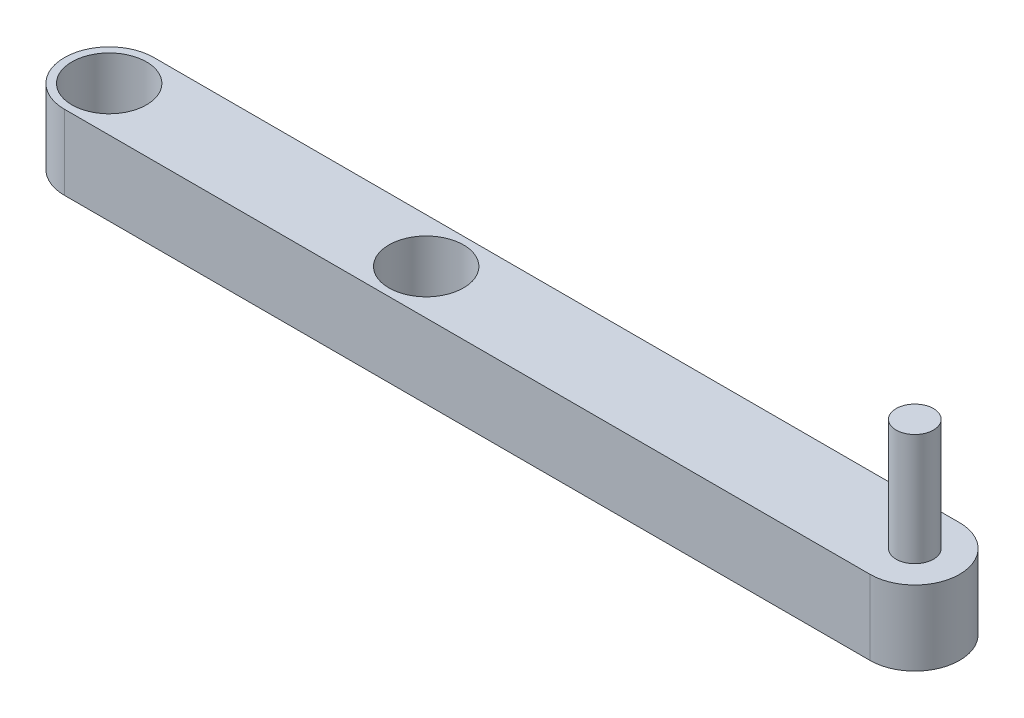
SolidWorks part; units mm, degrees
ref_plane "Front Plane" through (0, 0, 0) normal (0, 0, 1) x (1, 0, 0)
ref_plane "Top Plane" through (0, 0, 0) normal (0, 1, 0) x (1, 0, 0)
ref_plane "Right Plane" through (0, 0, 0) normal (1, 0, 0) x (0, 0, -1)
sketch "Sketch1" plane through (0, 0, 0) normal (0, 1, 0) x (1, 0, 0)
  line L0 (0, 0) -> (108, 0) construction
  line L1 (0, 6) -> (108, 6)
  line L2 (0, -6) -> (108, -6)
  arc A0 (0, 6) -> (0, -6) centre (0, 0) ccw
  arc A1 (108, -6) -> (108, 6) centre (108, 0) ccw
  circle A2 centre (0, 0) radius 5
  circle A3 centre (42.5, 0) radius 5
  point P3 (54, 0)
  dimension "D2" = 6
  dimension "D3" = 10
  dimension "D1" = 108
  dimension "D4" = 42.5
extrude "Boss-Extrude1" add sketch "Sketch1" along normal blind 10
sketch "Sketch2" plane through (0, 10, 0) normal (0, 1, 0) x (1, 0, 0)
  circle A0 centre (108, 0) radius 2.5
  dimension "D1" = 5
extrude "Boss-Extrude2" add sketch "Sketch2" along normal blind 15
